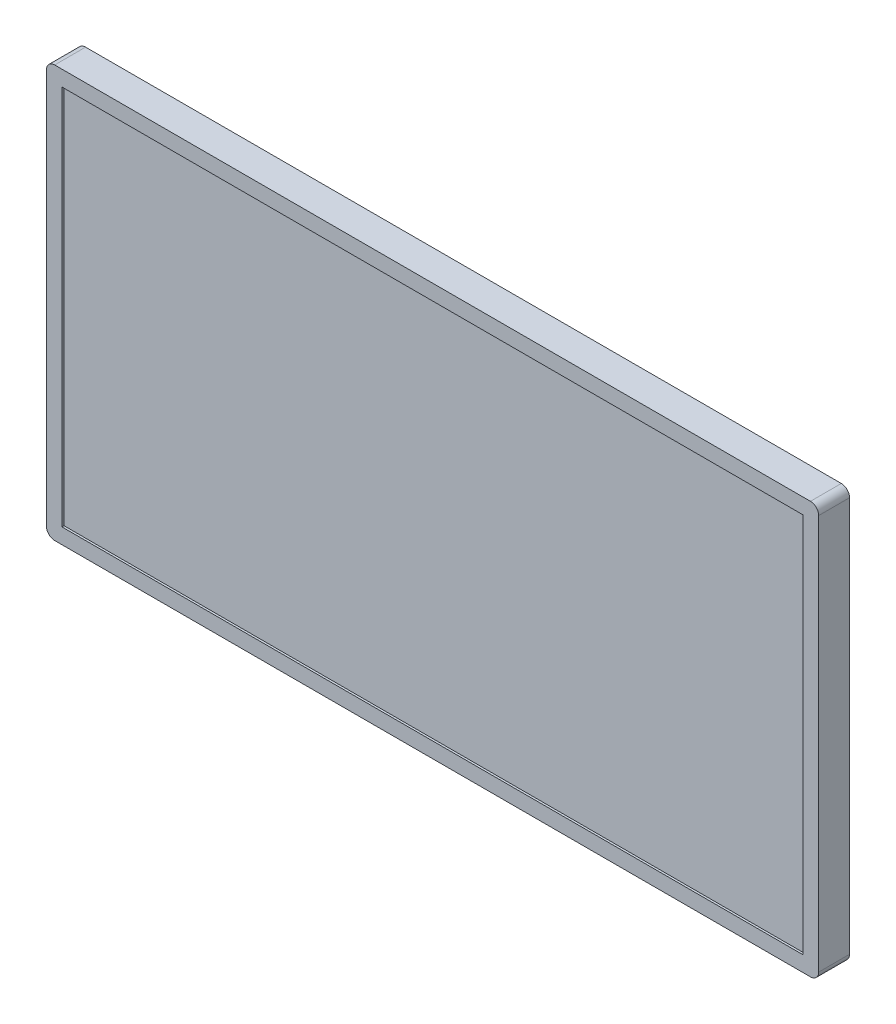
SolidWorks part; units mm, degrees
ref_plane "Alzado" through (0, 0, 0) normal (0, 0, 1) x (1, 0, 0)
ref_plane "Planta" through (0, 0, 0) normal (0, 1, 0) x (1, 0, 0)
ref_plane "Vista lateral" through (0, 0, 0) normal (1, 0, 0) x (0, 0, -1)
sketch "Croquis1" plane through (0, 0, 0) normal (0, 0, 1) x (1, 0, 0)
  line L1 (0, 0) -> (750, 0)
  line L2 (0, 0) -> (0, 400)
  line L3 (0, 400) -> (750, 400)
  line L4 (750, 0) -> (750, 400)
  dimension "D1" = 850
  dimension "D2" = 400
  dimension "D3" = 750
extrude "Saliente-Extruir1" add sketch "Croquis1" along normal blind 30
sketch "Croquis2" plane through (0, 0, 30) normal (0, 0, 1) x (1, 0, 0)
  line L0 (375, 400) -> (375, 0) construction
  line L1 (750, 400) -> (0, 400) construction
  line L2 (0, 0) -> (750, 0) construction
  line L3 (750, 0) -> (750, 400) construction
  line L4 (735, 15) -> (15, 15)
  line L5 (735, 15) -> (735, 385)
  line L6 (735, 385) -> (15, 385)
  line L7 (15, 15) -> (15, 385)
  line L8 (735, 15) -> (15, 385) construction
  line L9 (735, 385) -> (15, 15) construction
  point P6 (375, 200)
  dimension "D1" = 15
  dimension "D2" = 15
extrude "Cortar-Extruir1" cut sketch "Croquis2" against normal blind 2
fillet "Redondeo1" radius 8 4 edges at (0, 0, 15) (750, 0, 15) (750, 400, 15) (0, 400, 15)
